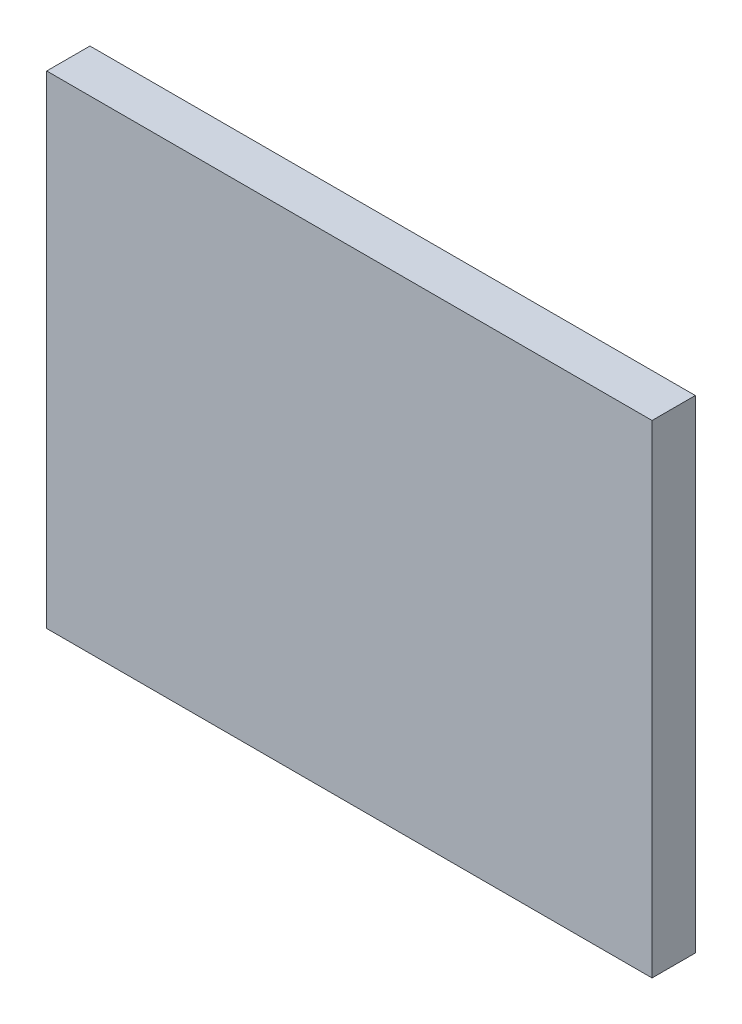
SolidWorks part; units mm, degrees
ref_plane "Front Plane" through (0, 0, 0) normal (0, 0, 1) x (1, 0, 0)
ref_plane "Top Plane" through (0, 0, 0) normal (0, 1, 0) x (1, 0, 0)
ref_plane "Right Plane" through (0, 0, 0) normal (1, 0, 0) x (0, 0, -1)
sketch "Sketch1" plane through (0, 0, 0) normal (0, 0, 1) x (1, 0, 0)
  line L1 (-21, 16.75) -> (21, 16.75)
  line L2 (-21, 16.75) -> (-21, -16.75)
  line L3 (-21, -16.75) -> (21, -16.75)
  line L4 (21, 16.75) -> (21, -16.75)
  line L5 (-21, 16.75) -> (21, -16.75) construction
  line L6 (-21, -16.75) -> (21, 16.75) construction
  point P0 (0, 0)
  dimension "D1" = 33.5
  dimension "D2" = 42
extrude "Boss-Extrude1" add sketch "Sketch1" along normal blind 3
